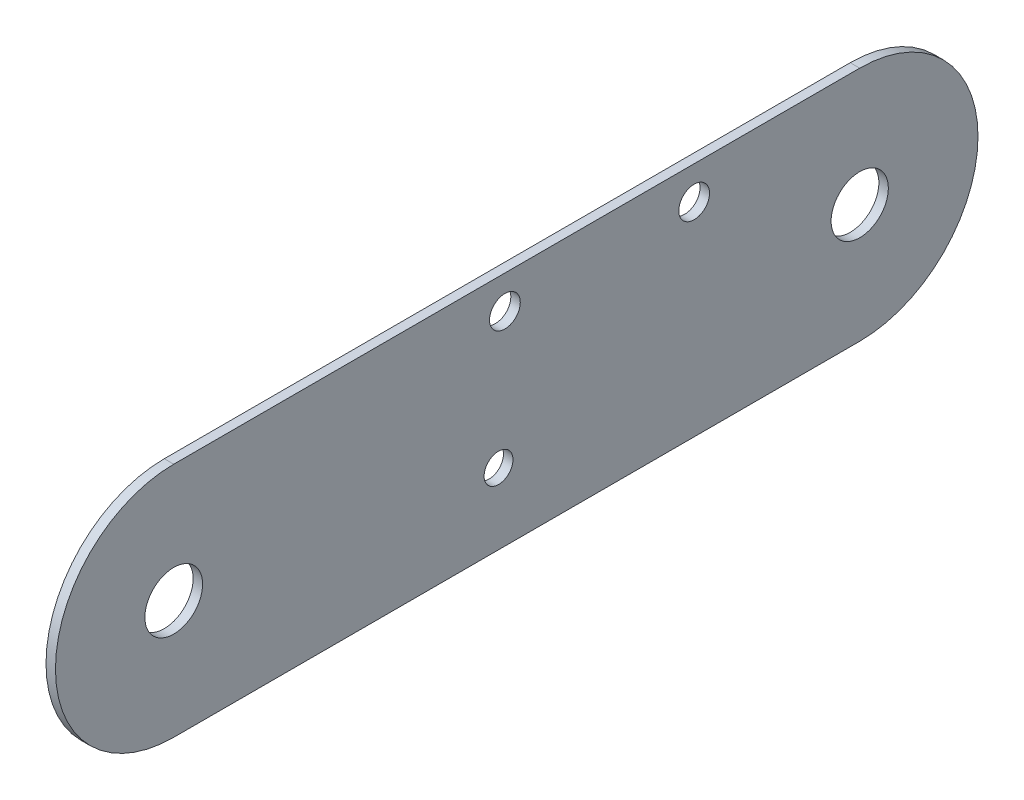
SolidWorks part; units mm, degrees
ref_plane "前视基准面" through (0, 0, 0) normal (0, 0, 1) x (1, 0, 0)
ref_plane "上视基准面" through (0, 0, 0) normal (0, 1, 0) x (1, 0, 0)
ref_plane "右视基准面" through (0, 0, 0) normal (1, 0, 0) x (0, 0, -1)
sketch "草图1" plane through (0, 0, 0) normal (1, 0, 0) x (0, 0, -1)
  line L0 (91.077, 40.4552) -> (33.8601, -58.6474) construction
  line L1 (19.4263, -58.6474) -> (-125.5737, -58.6474)
  line L2 (-134.9038, -36.1474) -> (137.7276, 121.2564) construction
  line L3 (23.3434, -40.432) -> (64.5291, -111.7676) construction
  line L4 (-240.8626, -64.5389) -> (49.2974, 13.2092) construction
  line L5 (140.7147, 124.2435) -> (-66.5738, -83.0449) construction
  line L6 (153.5693, 198.695) -> (-51.0405, -155.6994) construction
  line L7 (194.3644, -33.6474) -> (-306.5717, -33.6474) construction
  line L8 (69.4263, 52.9552) -> (-125.5737, -33.6474) construction
  line L9 (4.9926, -8.6474) -> (-125.5737, -8.6474)
  line L10 (47.7757, 65.4552) -> (4.9926, -8.6474) construction
  line L11 (137.7276, 121.2564) -> (91.077, 40.4552) construction
  line L12 (4.9926, -8.6474) -> (19.4263, -8.6474)
  line L13 (-184.3419, -15.6474) -> (79.5959, -15.6474) construction
  line L14 (-125.5737, -33.6474) -> (-125.5737, 86.0203) construction
  circle A0 centre (19.4263, -33.6474) radius 6.05
  circle A1 centre (-125.5737, -33.6474) radius 6.1
  circle A2 centre (69.4263, 52.9552) radius 3.25 construction
  arc A3 (91.077, 40.4552) -> (47.7757, 65.4552) centre (69.4263, 52.9552) ccw construction
  arc A4 (-125.5737, -8.6474) -> (-125.5737, -58.6474) centre (-125.5737, -33.6474) ccw
  circle A5 centre (-56.9216, -43.6474) radius 3.05
  arc A8 (19.4263, -58.6474) -> (19.4263, -8.6474) centre (19.4263, -33.6474) ccw
  circle A9 centre (-15.5737, -15.6474) radius 3.25
  circle A10 centre (-55.5737, -15.6474) radius 3.25
  point P10 (0, 0)
  point P17 (-125.5737, -33.6474)
  point P18 (69.4263, 52.9552)
  dimension "D6" = 12.1
  dimension "D8" = 12.2
  dimension "D10" = 6.5
  dimension "D13" = 6.1
  dimension "D14" = 77
  dimension "D15" = 15
  dimension "D16" = 50
  dimension "D18" = 6.5
  dimension "D19" = 40
  dimension "D20" = 70
  dimension "D2" = 120
  dimension "D3" = 30
  dimension "D4" = 15
  dimension "D5" = 15
  dimension "D7" = 207.735
  dimension "D9" = 100
  dimension "D11" = 50
  dimension "D12" = 145
  dimension "D17" = 18
extrude "凸台-拉伸1" add sketch "草图1" along normal blind 2
